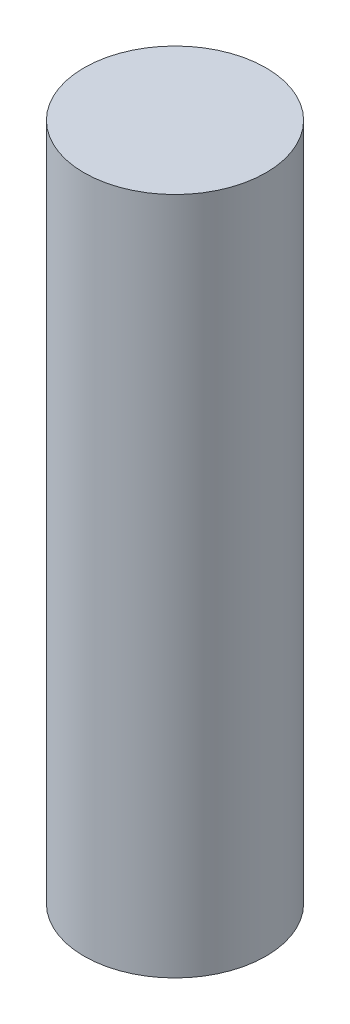
SolidWorks part; units mm, degrees
ref_plane "Front Plane" through (0, 0, 0) normal (0, 0, 1) x (1, 0, 0)
ref_plane "Top Plane" through (0, 0, 0) normal (0, 1, 0) x (1, 0, 0)
ref_plane "Right Plane" through (0, 0, 0) normal (1, 0, 0) x (0, 0, -1)
sketch "Sketch1" plane through (0, 0, 0) normal (0, 1, 0) x (1, 0, 0)
  circle A0 centre (0, 0) radius 9.21
  dimension "D1" = 18.42
extrude "Boss-Extrude1" add sketch "Sketch1" along normal blind 68.7
